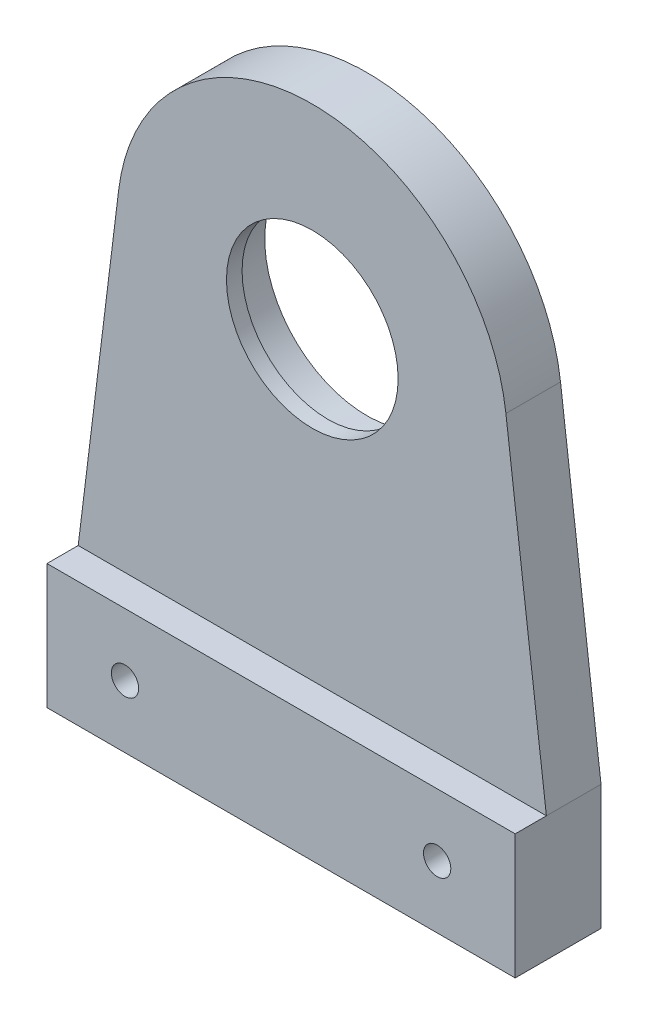
SolidWorks part; units mm, degrees
ref_plane "Front Plane" through (0, 0, 0) normal (0, 0, 1) x (1, 0, 0)
ref_plane "Top Plane" through (0, 0, 0) normal (0, 1, 0) x (1, 0, 0)
ref_plane "Right Plane" through (0, 0, 0) normal (1, 0, 0) x (0, 0, -1)
sketch "Sketch1" plane through (0, 0, 0) normal (0, 0, 1) x (1, 0, 0)
  line L0 (-30, -55) -> (30, -55)
  line L1 (-30, -55) -> (-30, -39)
  line L2 (-30, -39) -> (-24.812, 3.0605)
  line L3 (30, -55) -> (30, -39)
  line L4 (30, -39) -> (24.812, 3.0605)
  arc A0 (24.812, 3.0605) -> (-24.812, 3.0605) centre (0, 0) ccw
  circle A1 centre (0, 0) radius 13.1
  circle A2 centre (-20, -47) radius 1.75
  circle A3 centre (20, -47) radius 1.75
  point P6 (0, -55)
  point P14 (-30, -47)
  dimension "D1" = 50
  dimension "D2" = 26.2
  dimension "D8" = 3.5
  dimension "D3" = 55
  dimension "D4" = 60
  dimension "D5" = 39
  dimension "D6" = 10
  dimension "D7" = 10
extrude "Boss-Extrude1" add sketch "Sketch1" along normal blind 7
sketch "Sketch2" plane through (0, 0, 7) normal (0, 0, 1) x (1, 0, 0)
  circle A0 centre (0, 0) radius 11
  circle A1 centre (0, 0) radius 13.1 construction
  circle A2 centre (0, 0) radius 13.1
  dimension "D1" = 22
extrude "Boss-Extrude2" add sketch "Sketch2" against normal blind 2
sketch "Sketch3" plane through (0, 0, 7) normal (0, 0, 1) x (1, 0, 0)
  line L1 (-30, -55) -> (30, -55)
  line L2 (-30, -55) -> (-30, -39)
  line L3 (-30, -39) -> (30, -39)
  line L4 (30, -55) -> (30, -39)
  circle A0 centre (20, -47) radius 1.75 construction
  circle A1 centre (-20, -47) radius 1.75 construction
  circle A2 centre (20, -47) radius 1.75
  circle A3 centre (-20, -47) radius 1.75
extrude "Boss-Extrude3" add sketch "Sketch3" along normal blind 4
sketch "Sketch4" plane through (0, 0, 0) normal (0, 0, -1) x (-1, 0, 0)
  circle A0 centre (-20, -47) radius 3.75
  circle A1 centre (20, -47) radius 3.75
  dimension "D1" = 7.5
extrude "Cut-Extrude1" cut sketch "Sketch4" against normal blind 4
